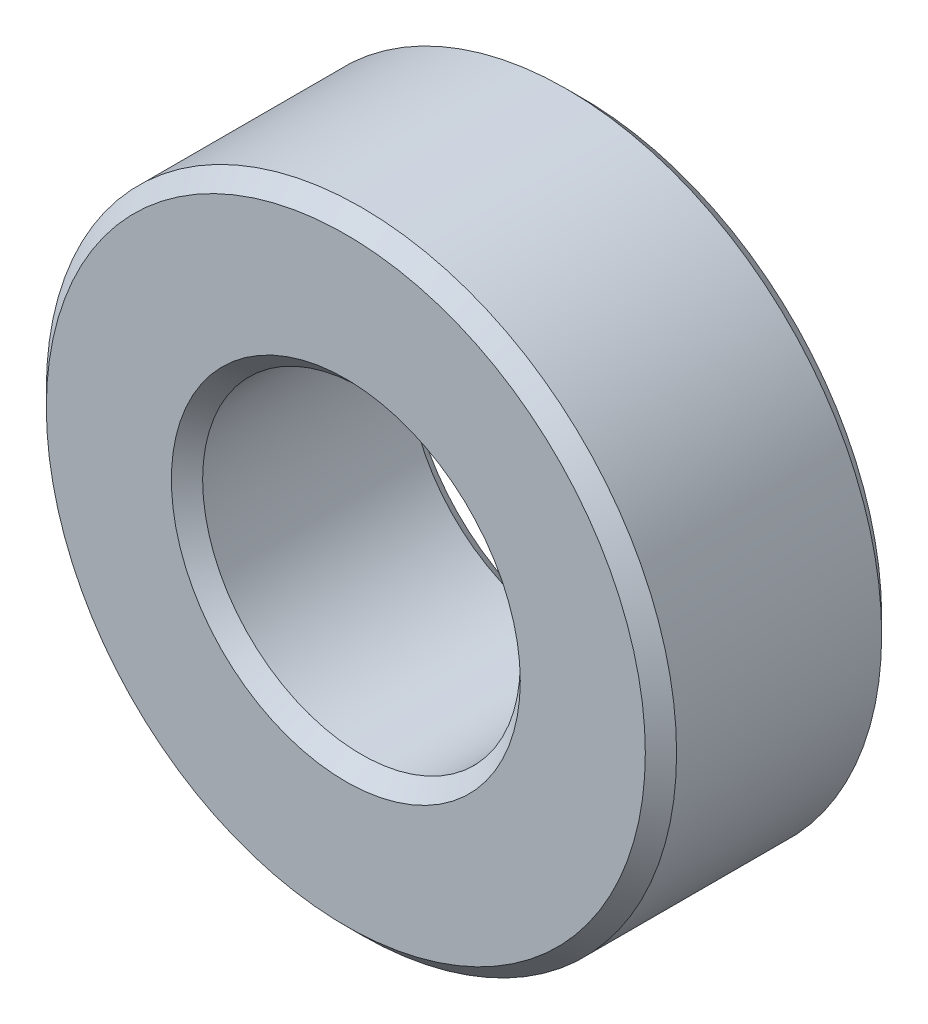
SolidWorks part; units mm, degrees
ref_plane "Front Plane" through (0, 0, 0) normal (0, 0, 1) x (1, 0, 0)
ref_plane "Top Plane" through (0, 0, 0) normal (0, 1, 0) x (1, 0, 0)
ref_plane "Right Plane" through (0, 0, 0) normal (1, 0, 0) x (0, 0, -1)
sketch "Sketch1" plane through (0, 0, 0) normal (0, 0, 1) x (1, 0, 0)
  circle A0 centre (0, 0) radius 6.35 construction
  circle A1 centre (0, 0) radius 3.2004 construction
  point P4 (0, 6.35)
  dimension "ID" = 6.4008
  dimension "OD" = 12.7
sketch "Sketch2" plane through (0, 0, 0) normal (1, 0, 0) x (0, 0, -1)
  line L0 (-2.3813, 6.35) -> (2.3813, 6.35) construction
  dimension "Length" = 4.7625
sketch "Sketch3" plane through (0, 0, 0) normal (0, 0, 1) x (1, 0, 0)
  circle A0 centre (0, 0) radius 3.2004 construction
  circle A1 centre (0, 0) radius 6.35 construction
  circle A2 centre (0, 0) radius 3.2004
  circle A3 centre (0, 0) radius 6.35
extrude "Boss-Extrude1" add sketch "Sketch3" against normal up to vertex (2.3813 mm away) and the other way up to vertex (2.3813 mm away) up to point (0, 6.35, -2.3813) other way up to point (0, 6.35, 2.3813)
chamfer "Chamfer1" distance 0.315 angle 45 1 edges at (6.35, 0, 2.3813)
equation "\"D1@Chamfer1\"=(\"OD@Sketch1\"-\"ID@Sketch1\")*0.05"
